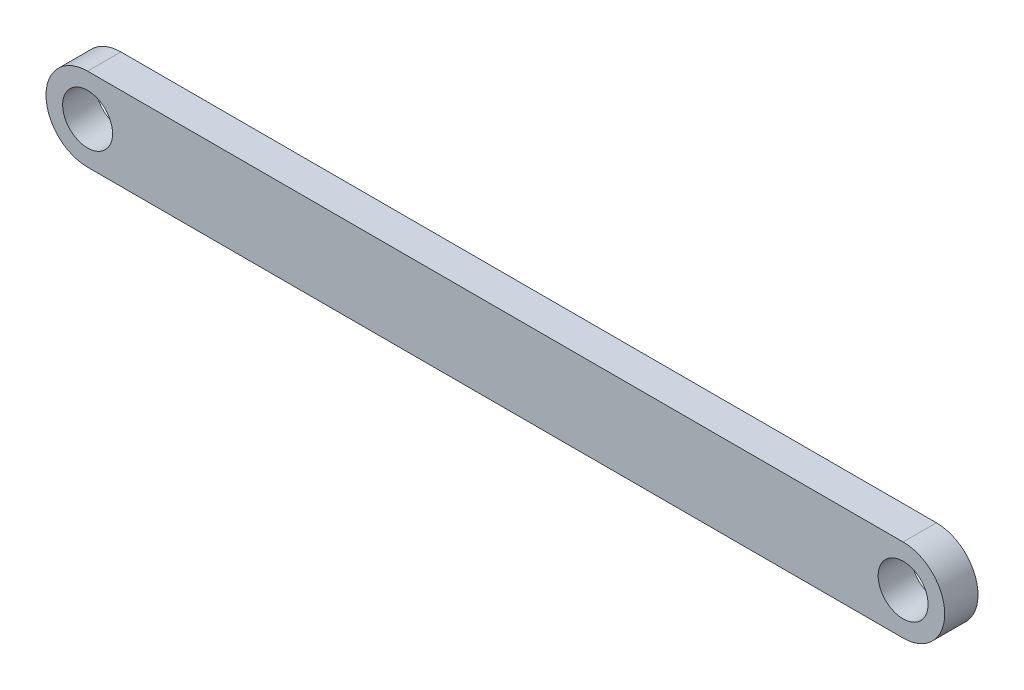
SolidWorks part; units mm, degrees
ref_plane "Front Plane" through (0, 0, 0) normal (0, 0, 1) x (1, 0, 0)
ref_plane "Top Plane" through (0, 0, 0) normal (0, 1, 0) x (1, 0, 0)
ref_plane "Right Plane" through (0, 0, 0) normal (1, 0, 0) x (0, 0, -1)
sketch "Sketch1" plane through (0, 0, 0) normal (0, 0, 1) x (1, 0, 0)
  line L0 (0.0558, -0.1678) -> (49.0558, -0.1678) construction
  line L1 (0.0558, 2.3322) -> (49.0558, 2.3322)
  line L2 (0.0558, -2.6678) -> (49.0558, -2.6678)
  arc A0 (0.0558, 2.3322) -> (0.0558, -2.6678) centre (0.0558, -0.1678) ccw
  arc A1 (49.0558, -2.6678) -> (49.0558, 2.3322) centre (49.0558, -0.1678) ccw
  circle A2 centre (0.0558, -0.1678) radius 1.5
  circle A3 centre (49.0558, -0.1678) radius 1.5
  point P2 (24.5558, -0.1678)
  dimension "D3" = 3
  dimension "D4" = 3
  dimension "D1" = 49
  dimension "D2" = 5
extrude "Boss-Extrude1" add sketch "Sketch1" along normal blind 2
